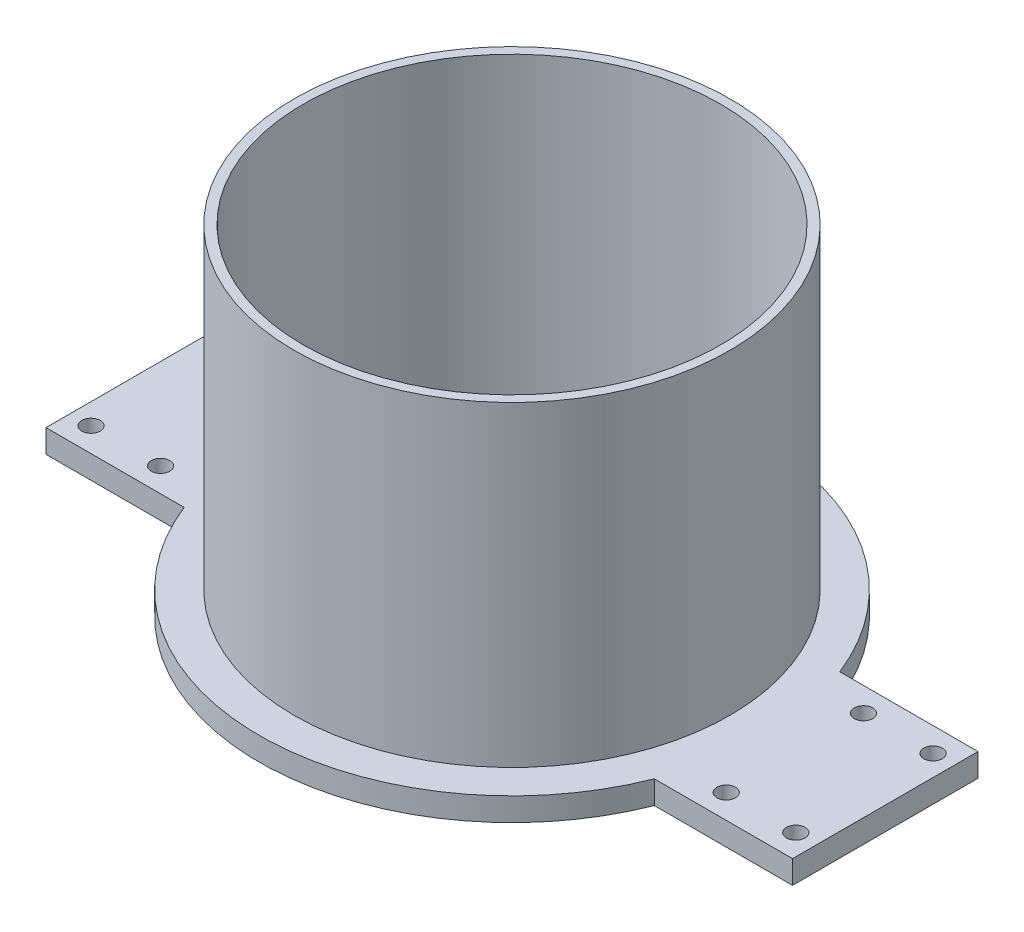
SolidWorks part; units mm, degrees
material "ABS"
ref_plane "Front" through (0, 0, 0) normal (0, 0, 1) x (1, 0, 0)
ref_plane "Top" through (0, 0, 0) normal (0, 1, 0) x (1, 0, 0)
ref_plane "Right" through (0, 0, 0) normal (1, 0, 0) x (0, 0, -1)
sketch "草图1" plane through (0, 0, 0) normal (0, 1, 0) x (1, 0, 0)
  line L0 (80.5, 0) -> (56.5, 0) construction
  line L1 (56.5, 0) -> (56.5, 20) construction
  line L2 (56.5, 0) -> (56.5, -20) construction
  line L3 (68.5, 0) -> (68.5, -14.8) construction
  line L4 (68.5, -14.8) -> (61, -14.8) construction
  line L5 (68.5, -14.8) -> (76, -14.8) construction
  line L6 (56.5, 0) -> (54.5, 0) construction
  line L7 (80.5, 0) -> (80.5, 20) construction
  line L8 (80.5, 20) -> (50.6976, 20) construction
  line L9 (50.6976, 20) -> (80.5, 20)
  line L10 (80.5, 20) -> (80.5, -20)
  line L11 (80.5, -20) -> (50.6976, -20)
  line L12 (0, 0) -> (0, 45) construction
  line L13 (-80.5, -20) -> (-50.6976, -20)
  line L14 (-80.5, 20) -> (-80.5, -20)
  line L15 (-50.6976, 20) -> (-80.5, 20)
  arc A0 (50.6976, 20) -> (-50.6976, 20) centre (0, 0) ccw
  circle A1 centre (0, 0) radius 45
  circle A3 centre (76, -14.8) radius 2
  circle A6 centre (61, -14.8) radius 2
  circle A7 centre (76, 14.8) radius 2
  circle A8 centre (61, 14.8) radius 2
  circle A9 centre (-61, 14.8) radius 2
  circle A10 centre (-76, 14.8) radius 2
  circle A11 centre (-76, -14.8) radius 2
  circle A12 centre (-61, -14.8) radius 2
  arc A13 (-50.6976, -20) -> (50.6976, -20) centre (0, 0) ccw
extrude "凸台-拉伸1" add sketch "草图1" along normal blind 5
sketch "草图2" plane through (0, 5, 0) normal (0, 1, 0) x (1, 0, 0)
  circle A0 centre (0, 0) radius 45
  circle A1 centre (0, 0) radius 47
extrude "凸台-拉伸2" add sketch "草图2" along normal blind 68.18
